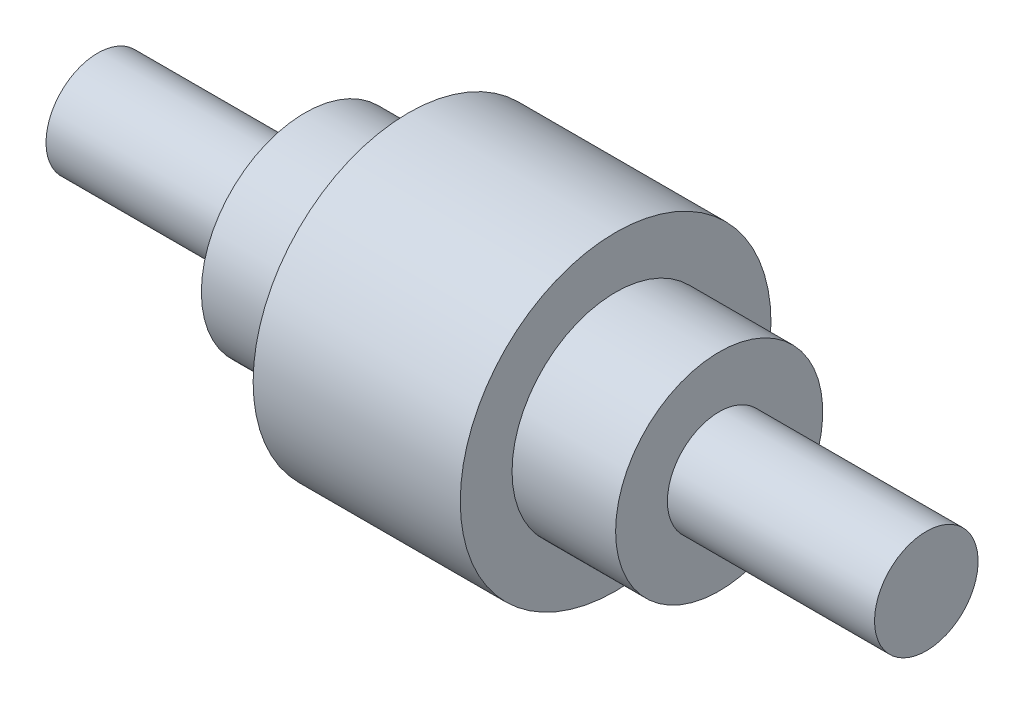
SolidWorks part; units mm, degrees
ref_plane "Front Plane" through (0, 0, 0) normal (0, 0, 1) x (1, 0, 0)
ref_plane "Top Plane" through (0, 0, 0) normal (0, 1, 0) x (1, 0, 0)
ref_plane "Right Plane" through (0, 0, 0) normal (1, 0, 0) x (0, 0, -1)
sketch "Sketch2" plane through (0, 0, 0) normal (0, 0, 1) x (1, 0, 0)
  line L0 (0, 0) -> (0, 50)
  line L1 (-150, 0) -> (150, 0) construction
  line L2 (-30, 50) -> (30, 50)
  line L3 (30, 50) -> (30, 30)
  line L4 (30, 30) -> (70, 30)
  line L5 (70, 30) -> (70, 10)
  line L6 (70, 10) -> (150, 10)
  line L7 (150, 10) -> (150, 0)
  line L8 (-150, 10) -> (-150, 0)
  line L9 (-70, 10) -> (-150, 10)
  line L10 (-70, 30) -> (-70, 10)
  line L11 (-30, 30) -> (-70, 30)
  line L12 (-30, 50) -> (-30, 30)
  dimension "D1" = 50
  dimension "D2" = 30
  dimension "D3" = 20
  dimension "D4" = 40
  dimension "D5" = 20
  dimension "D6" = 80
revolve "Revolve-Thin2" add sketch "Sketch2" angle 360 about L1
